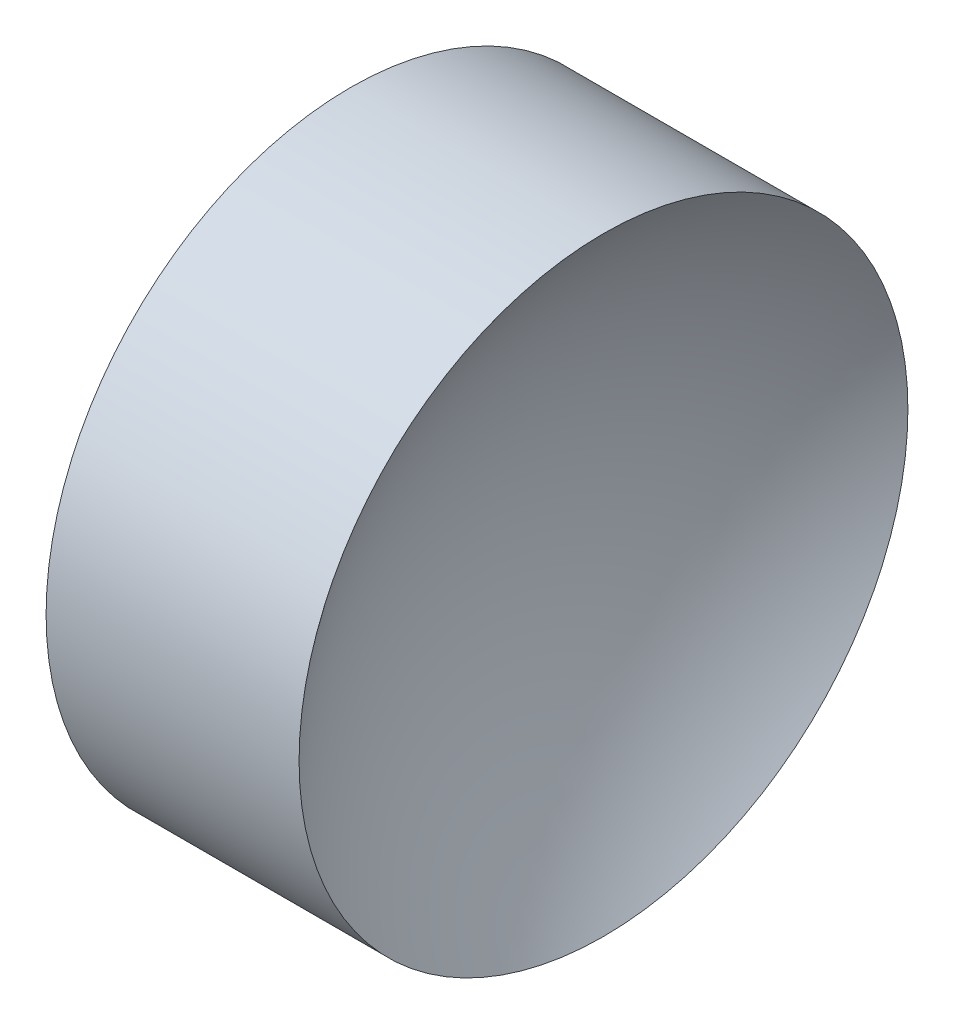
SolidWorks part; units mm, degrees
ref_plane "前视基准面" through (0, 0, 0) normal (0, 0, 1) x (1, 0, 0)
ref_plane "上视基准面" through (0, 0, 0) normal (0, 1, 0) x (1, 0, 0)
ref_plane "右视基准面" through (0, 0, 0) normal (1, 0, 0) x (0, 0, -1)
sketch "草图1" plane through (0, 0, 0) normal (0, 0, 1) x (1, 0, 0)
  line L0 (363.5086, 112.5921) -> (375.4042, 112.5921) construction
  line L1 (366.5624, 112.5921) -> (366.5624, 118.8421)
  line L2 (366.5624, 118.8421) -> (371.7562, 118.8421)
  line L3 (369.5624, 112.5921) -> (366.5624, 112.5921)
  arc A0 (371.7562, 118.8421) -> (369.5624, 112.5921) centre (379.5624, 112.5921) ccw
  dimension "D2" = 10
  dimension "D1" = 5.1938
  dimension "D3" = 3
revolve "旋转1" add sketch "草图1" angle 360 about L0
